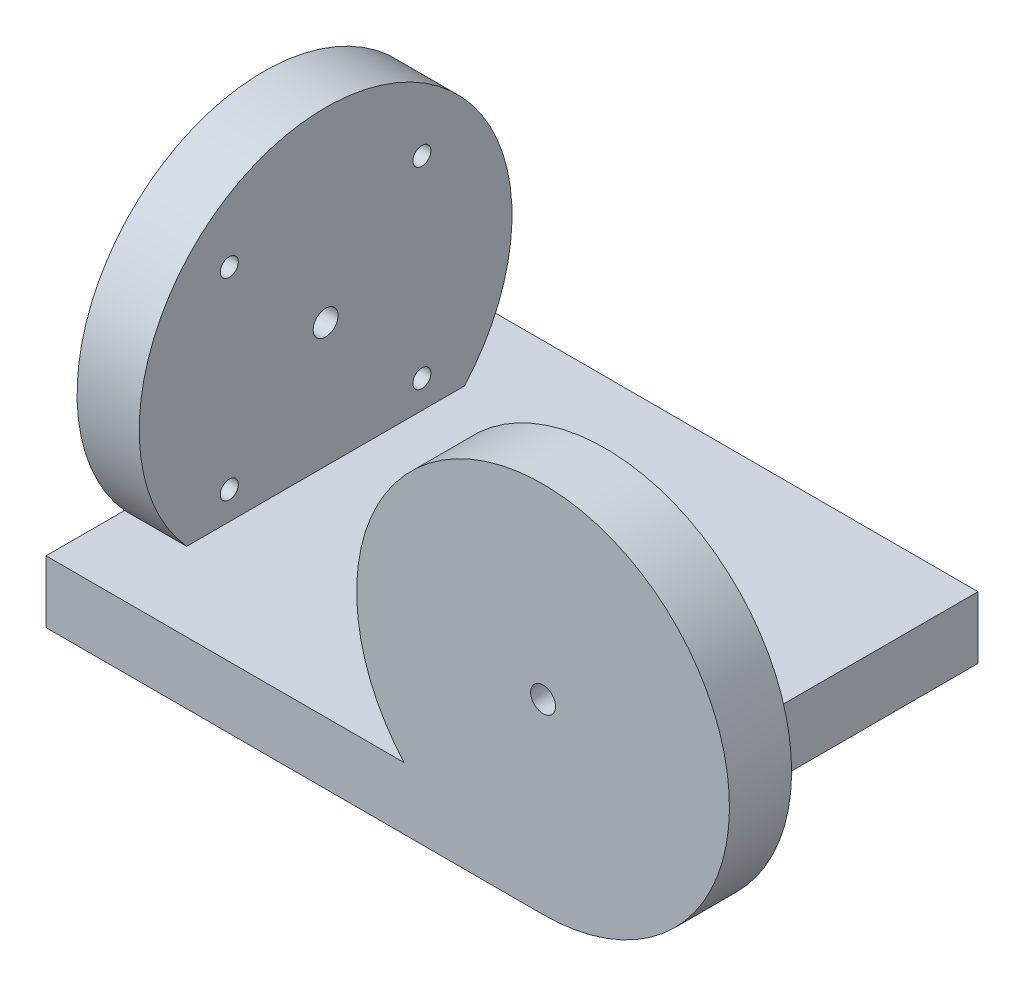
SolidWorks part; units mm, degrees
ref_plane "Front Plane" through (0, 0, 0) normal (0, 0, 1) x (1, 0, 0)
ref_plane "Top Plane" through (0, 0, 0) normal (0, 1, 0) x (1, 0, 0)
ref_plane "Right Plane" through (0, 0, 0) normal (1, 0, 0) x (0, 0, -1)
sketch "Sketch1" plane through (0, 0, 0) normal (0, 0, 1) x (1, 0, 0)
  circle A0 centre (0, 0) radius 30
  dimension "D1" = 60
extrude "Boss-Extrude1" add sketch "Sketch1" along normal blind 10
sketch "Sketch2" plane through (0, 0, 10) normal (0, 0, 1) x (1, 0, 0)
  line L1 (0, -30) -> (-80, -30)
  line L2 (0, -30) -> (0, -20)
  line L3 (0, -20) -> (-80, -20)
  line L4 (-80, -30) -> (-80, -20)
  circle A0 centre (0, 0) radius 30 construction
  dimension "D1" = 10
  dimension "D2" = 80
extrude "Boss-Extrude2" add sketch "Sketch2" against normal blind 70
sketch "Sketch3" plane through (-80, 0, 0) normal (-1, 0, 0) x (0, 0, 1)
  line L0 (-60, -20) -> (10, -20) construction
  line L1 (-60, -30) -> (10, -30) construction
  circle A0 centre (-25, 0) radius 30
  point P5 (-25, -20)
  dimension "D1" = 60
extrude "Boss-Extrude3" add sketch "Sketch3" against normal blind 10
hole_wizard "Ø4.0mm Dowel Hole1" positions "Sketch8" profile "Sketch9" hole size "Ø4.0" standard "ANSI Metric"
sketch "Sketch8" plane through (0, 0, 0) normal (0, 0, -1) x (-1, 0, 0)
  point P0 (0, 0)
sketch "Sketch9" plane through (0, 0, 0) normal (1, 0, 0) x (0, 1, 0)
  line L0 (0, 0) -> (0, 11.3017)
  line L1 (0, 11.3017) -> (2, 10.1)
  line L2 (2, 10.1) -> (2, 0)
  line L5 (2, 0) -> (0, 0)
  line L10 (0, 11.3017) -> (-2, 10.1) construction
  line L11 (0, -6.35) -> (0, 107.95) construction
  dimension "Hole Dia." = 4
  dimension "Hole Depth" = 10.1
  dimension "Drill Angle" = 118
hole_wizard "M3.5x0.6 Tapped Hole1" positions "Sketch10" profile "Sketch11" tap size "M3.5x0.6" standard "ANSI Metric"
sketch "Sketch10" plane through (0, 0, 0) normal (0, 0, -1) x (-1, 0, 0)
  point P0 (-15.5, 15.5)
  point P2 (15.5, 15.5)
  point P4 (15.5, -15.5)
  point P6 (-15.5, -15.5)
  dimension "D1" = 31
  dimension "D2" = 31
  dimension "D3" = 15.5
  dimension "D4" = 15.5
sketch "Sketch11" plane through (15.5, 15.5, 0) normal (1, 0, 0) x (0, 1, 0)
  line L0 (0, 0) -> (0, 9.6712)
  line L1 (0, 9.6712) -> (1.45, 8.8)
  line L2 (1.45, 8.8) -> (1.45, 0)
  line L5 (1.45, 0) -> (0, 0)
  line L10 (0, 9.6712) -> (-1.45, 8.8) construction
  line L11 (0, -6.35) -> (0, 107.95) construction
  dimension "Tap Drill Dia." = 2.9
  dimension "Tap Drill Depth" = 8.8
  dimension "Drill Angle" = 118
cosmetic thread "Hole Thread5" parameters "D1"=7, "D2"=3.5
cosmetic thread "Hole Thread6" parameters "D1"=7, "D2"=3.5
cosmetic thread "Hole Thread7" parameters "D1"=7, "D2"=3.5
cosmetic thread "Hole Thread8" parameters "D1"=7, "D2"=3.5
hole_wizard "Ø4.0mm Dowel Hole5" positions "Sketch33" profile "Sketch35" hole size "Ø4.0" standard "ANSI Metric"
sketch "Sketch33" plane through (-70, 13.4986, 45.9848) normal (1, 0, 0) x (0, 0, -1)
  point P0 (70.9848, -13.4986)
sketch "Sketch35" plane through (-70, 0, -25) normal (0, 1, 0) x (0, 0, -1)
  line L0 (0, 0) -> (0, 11.3017)
  line L1 (0, 11.3017) -> (2, 10.1)
  line L2 (2, 10.1) -> (2, 0)
  line L5 (2, 0) -> (0, 0)
  line L10 (0, 11.3017) -> (-2, 10.1) construction
  line L11 (0, -6.35) -> (0, 107.95) construction
  dimension "Hole Dia." = 4
  dimension "Hole Depth" = 10.1
  dimension "Drill Angle" = 118
hole_wizard "M3.5x0.6 Tapped Hole4" positions "Sketch37" profile "Sketch39" tap size "M3.5x0.6" standard "ANSI Metric"
sketch "Sketch37" plane through (-70, 0.7433, -25.0568) normal (1, 0, 0) x (0, 0, -1)
  line L0 (2.9687, -0.7433) -> (-4.5438, -0.7433) construction
  line L2 (-0.0568, -0.7433) -> (-0.0568, -5.0259) construction
  point P0 (-15.5568, 14.7567)
  point P2 (15.4432, 14.7567)
  point P4 (15.4432, -16.2433)
  point P6 (-15.5568, -16.2433)
  dimension "D1" = 31
  dimension "D2" = 31
  dimension "D3" = 15.5
  dimension "D4" = 15.5
sketch "Sketch39" plane through (-70, 15.5, -9.5) normal (0, 1, 0) x (0, 0, -1)
  line L0 (0, 0) -> (0, 9.6712)
  line L1 (0, 9.6712) -> (1.45, 8.8)
  line L2 (1.45, 8.8) -> (1.45, 0)
  line L5 (1.45, 0) -> (0, 0)
  line L10 (0, 9.6712) -> (-1.45, 8.8) construction
  line L11 (0, -6.35) -> (0, 107.95) construction
  dimension "Tap Drill Dia." = 2.9
  dimension "Tap Drill Depth" = 8.8
  dimension "Drill Angle" = 118
cosmetic thread "Hole Thread18" parameters "D1"=7, "D2"=3.5
cosmetic thread "Hole Thread21" parameters "D1"=7, "D2"=3.5
cosmetic thread "Hole Thread22" parameters "D1"=7, "D2"=3.5
cosmetic thread "Hole Thread23" parameters "D1"=7, "D2"=3.5
